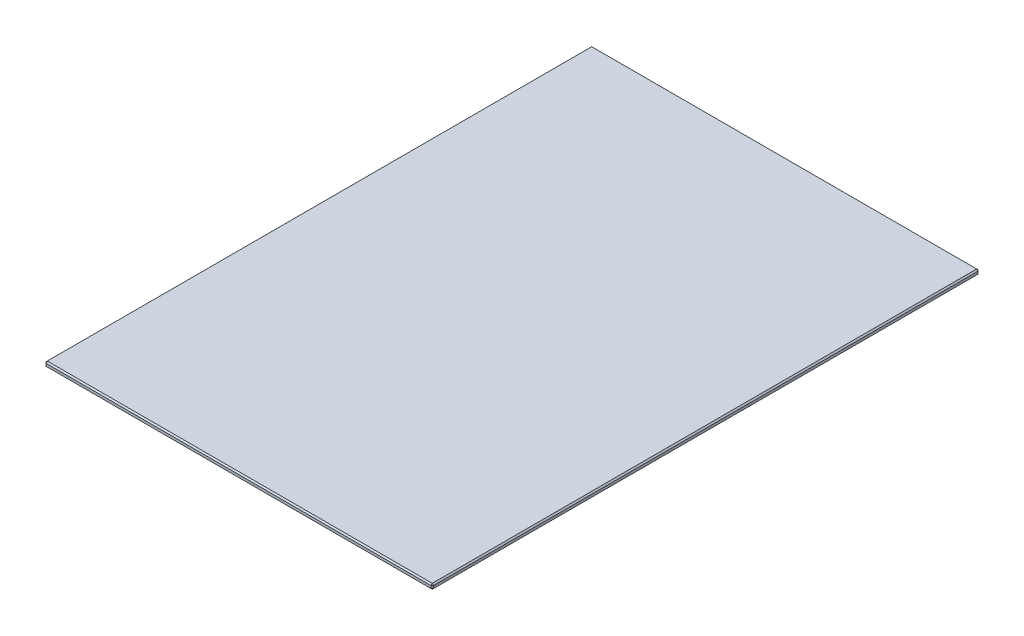
SolidWorks part; units mm, degrees
material "Glass"
ref_plane "Alzado" through (0, 0, 0) normal (0, 0, 1) x (1, 0, 0)
ref_plane "Planta" through (0, 0, 0) normal (0, 1, 0) x (1, 0, 0)
ref_plane "Vista lateral" through (0, 0, 0) normal (1, 0, 0) x (0, 0, -1)
sketch "Croquis1" plane through (0, 0, 0) normal (0, 1, 0) x (1, 0, 0)
  line L0 (-149.5, 211) -> (149.5, -211) construction
  line L1 (-149.5, -211) -> (149.5, -211)
  line L2 (-149.5, -211) -> (-149.5, 211)
  line L3 (-149.5, 211) -> (149.5, 211)
  line L4 (149.5, -211) -> (149.5, 211)
  dimension "D1" = 422
  dimension "D2" = 299
extrude "Saliente-Extruir1" add sketch "Croquis1" along normal blind 4
chamfer "Chaflán1" distance 1 angle 45 12 edges at (0, 0, 211) (149.5, 0, 0) (0, 0, -211) (-149.5, 0, 0) (0, 4, -211) (149.5, 4, 0) (0, 4, 211) (-149.5, 4, 0) (149.5, 2, -211) (149.5, 2, 211) (-149.5, 2, -211) (-149.5, 2, 211)
